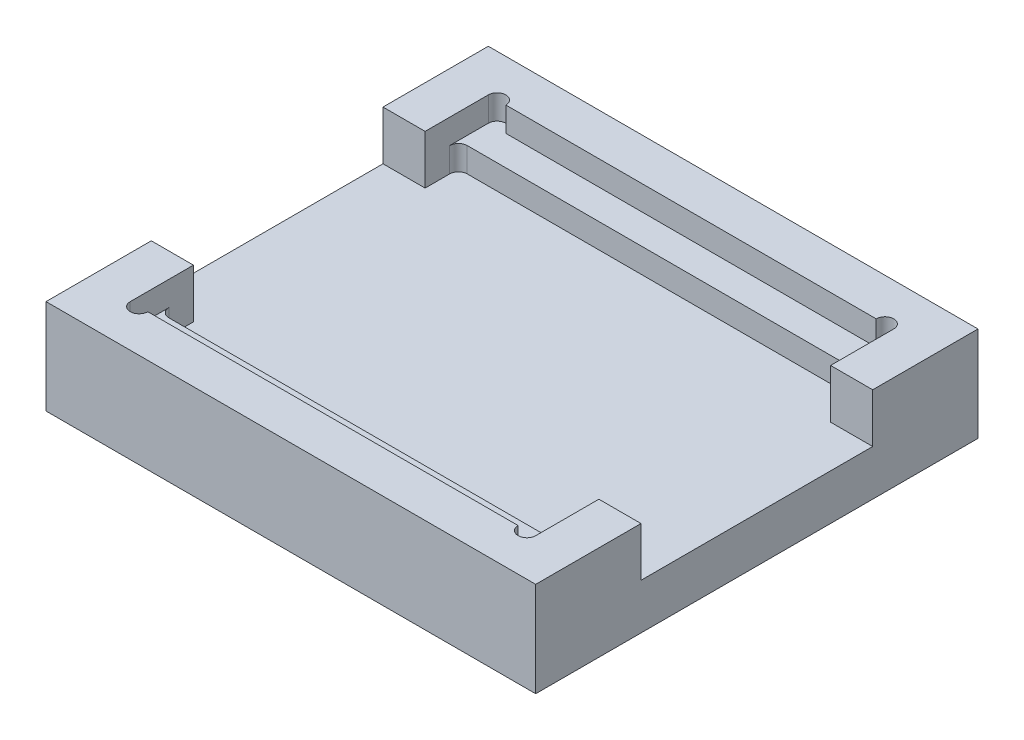
SolidWorks part; units mm, degrees
material "Delrin 2700 NC010, Low Viscosity Acetal Copolymer (SS)"
ref_plane "Front Plane" through (0, 0, 0) normal (0, 0, 1) x (1, 0, 0)
ref_plane "Top Plane" through (0, 0, 0) normal (0, 1, 0) x (1, 0, 0)
ref_plane "Right Plane" through (0, 0, 0) normal (1, 0, 0) x (0, 0, -1)
sketch "Sketch1" plane through (0, 0, 0) normal (0, 1, 0) x (1, 0, 0)
  line L1 (0, 0) -> (139.5, 0)
  line L2 (0, 0) -> (0, 126)
  line L3 (0, 126) -> (139.5, 126)
  line L4 (139.5, 0) -> (139.5, 126)
  dimension "D1" = 126
  dimension "D2" = 139.5
extrude "Boss-Extrude1" add sketch "Sketch1" along normal blind 27
sketch "Sketch2" plane through (0, 27, 0) normal (0, 1, 0) x (1, 0, 0)
  line L0 (0, 126) -> (0, 0) construction
  line L1 (12, 114) -> (127.5, 114)
  line L2 (12, 114) -> (12, 12)
  line L3 (12, 12) -> (127.5, 12)
  line L4 (127.5, 114) -> (127.5, 12)
  line L5 (0, 0) -> (139.5, 0) construction
  line L6 (139.5, 0) -> (139.5, 126) construction
  line L7 (139.5, 126) -> (0, 126) construction
  dimension "D1" = 12
  dimension "D2" = 12
  dimension "D3" = 12
  dimension "D4" = 12
extrude "Cut-Extrude1" cut sketch "Sketch2" against normal blind 7
sketch "Sketch3" plane through (0, 20, 0) normal (0, 1, 0) x (1, 0, 0)
  line L1 (127.5, 105.5) -> (12, 105.5)
  line L2 (127.5, 105.5) -> (127.5, 20.5)
  line L3 (127.5, 20.5) -> (12, 20.5)
  line L4 (12, 105.5) -> (12, 20.5)
  line L5 (127.5, 114) -> (12, 114) construction
  line L6 (12, 114) -> (12, 12) construction
  line L7 (127.5, 12) -> (127.5, 114) construction
  line L8 (12, 12) -> (127.5, 12) construction
  dimension "D1" = 8.5
  dimension "D3" = 8.5
extrude "Cut-Extrude2" cut sketch "Sketch3" against normal blind 7
sketch "Sketch4" plane through (0, 27, 0) normal (0, 1, 0) x (1, 0, 0)
  line L0 (0, 126) -> (0, 0) construction
  line L1 (0, 30) -> (12, 30)
  line L2 (0, 30) -> (0, 96)
  line L3 (0, 96) -> (12, 96)
  line L4 (12, 30) -> (12, 96)
  line L5 (12, 114) -> (12, 12) construction
  line L6 (0, 0) -> (139.5, 0) construction
  line L7 (139.5, 126) -> (0, 126) construction
  dimension "D1" = 30
  dimension "D2" = 30
extrude "Cut-Extrude3" cut sketch "Sketch4" against normal blind 14
sketch "Sketch5" plane through (0, 27, 0) normal (0, 1, 0) x (1, 0, 0)
  line L0 (139.5, 0) -> (139.5, 126) construction
  line L1 (139.5, 96) -> (127.5, 96)
  line L2 (139.5, 96) -> (139.5, 30)
  line L3 (139.5, 30) -> (127.5, 30)
  line L4 (127.5, 96) -> (127.5, 30)
  line L5 (127.5, 12) -> (127.5, 114) construction
  line L6 (0, 0) -> (139.5, 0) construction
  line L7 (139.5, 126) -> (0, 126) construction
  dimension "D1" = 30
  dimension "D2" = 30
extrude "Cut-Extrude4" cut sketch "Sketch5" against normal blind 14
sketch "Sketch6" plane through (0, 27, 0) normal (0, 1, 0) x (1, 0, 0)
  line L2 (12, 12) -> (127.5, 12) construction
  line L3 (12, 12) -> (17, 12)
  line L4 (12, 12) -> (127.5, 12) construction
  line L5 (122.5, 12) -> (127.5, 12)
  line L6 (127.5, 114) -> (12, 114) construction
  line L7 (12, 114) -> (17, 114)
  line L8 (122.5, 114) -> (127.5, 114)
  arc A1 (12, 12) -> (17, 12) centre (14.5, 12) ccw
  arc A2 (127.5, 12) -> (122.5, 12) centre (125, 12) cw
  arc A3 (12, 114) -> (17, 114) centre (14.5, 114) cw
  arc A4 (127.5, 114) -> (122.5, 114) centre (125, 114) ccw
  dimension "D1" = 2.5
  dimension "D2" = 2.5
  dimension "D3" = 2.5
  dimension "D4" = 2.5
extrude "Cut-Extrude5" cut sketch "Sketch6" against normal up to surface (7 mm away) up to face at (69.75, 20, -16.25)
fillet "Fillet1" radius 2.5 4 edges at (127.5, 16.5, -105.5) (127.5, 16.5, -20.5) (12, 16.5, -20.5) (12, 16.5, -105.5)
